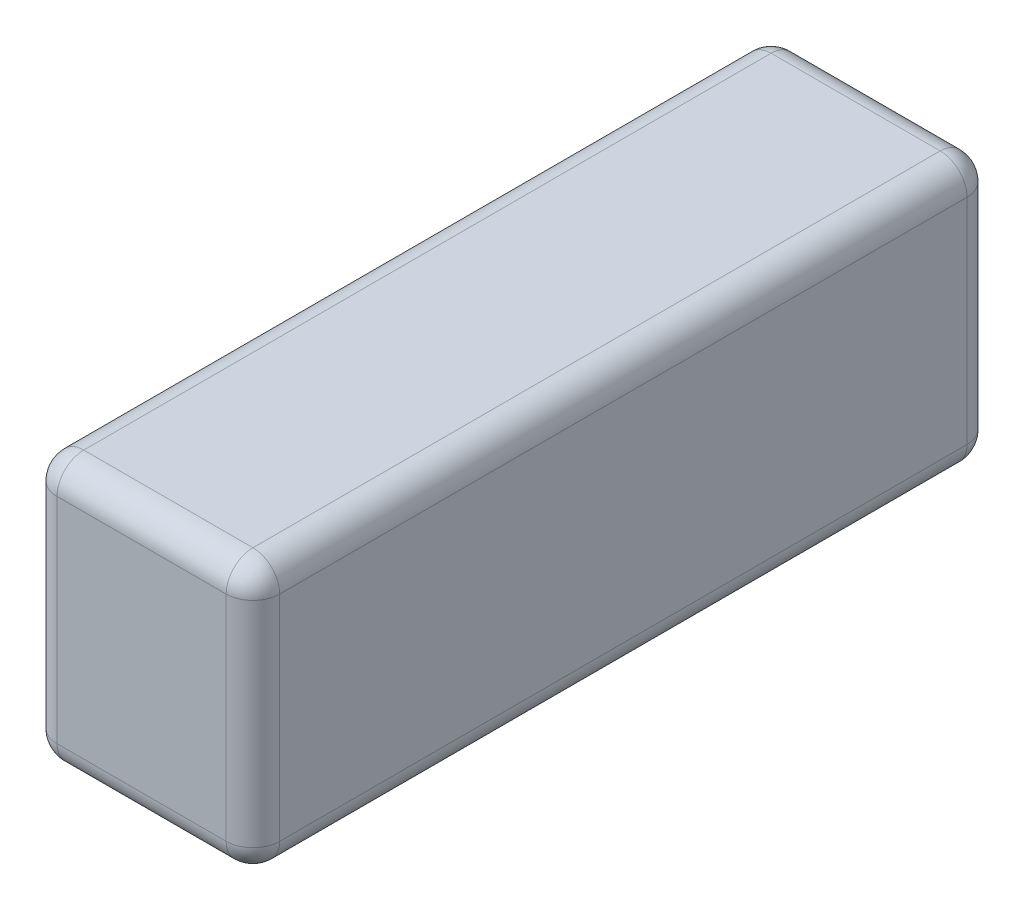
SolidWorks part; units mm, degrees
ref_plane "Front Plane" through (0, 0, 0) normal (0, 0, 1) x (1, 0, 0)
ref_plane "Top Plane" through (0, 0, 0) normal (0, 1, 0) x (1, 0, 0)
ref_plane "Right Plane" through (0, 0, 0) normal (1, 0, 0) x (0, 0, -1)
sketch "Sketch1" plane through (0, 0, 0) normal (1, 0, 0) x (0, 0, -1)
  line L1 (-21.971, -7.9375) -> (21.971, -7.9375)
  line L2 (-21.971, -7.9375) -> (-21.971, 7.9375)
  line L3 (-21.971, 7.9375) -> (21.971, 7.9375)
  line L4 (21.971, -7.9375) -> (21.971, 7.9375)
  point P4 (-21.971, 0)
  point P5 (0, 7.9375)
  dimension "D1" = 43.942
  dimension "D2" = 15.875
extrude "Boss-Extrude1" add sketch "Sketch1" along normal blind 13.208
fillet "Fillet1" radius 1.5875 12 edges at (0, 0, -21.971) (6.604, -7.9375, -21.971) (0, -7.9375, 0) (6.604, 7.9375, -21.971) (0, 7.9375, 0) (6.604, 7.9375, 21.971) (6.604, -7.9375, 21.971) (0, 0, 21.971) (13.208, 7.9375, 0) (13.208, 0, -21.971) (13.208, -7.9375, 0) (13.208, 0, 21.971)
